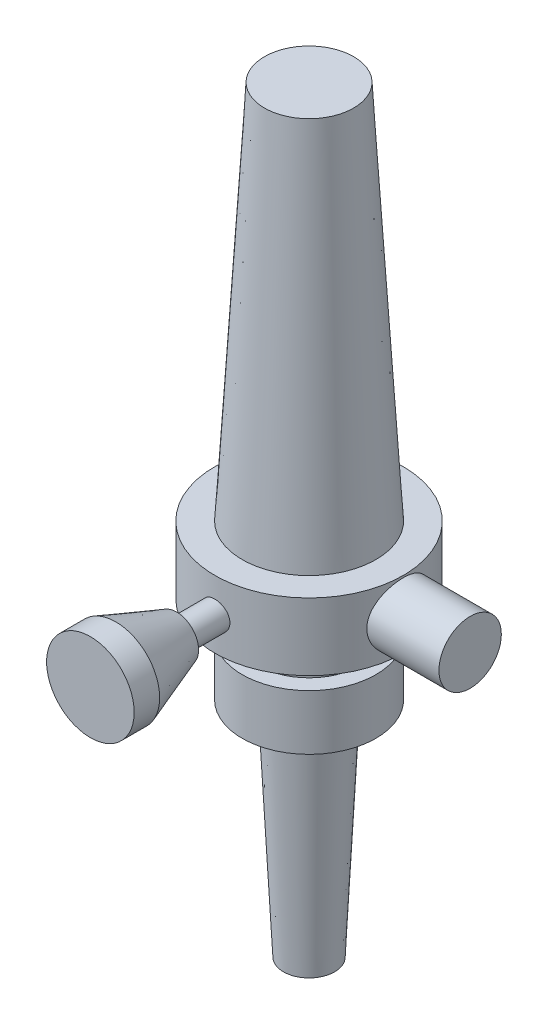
SolidWorks part; units mm, degrees
ref_plane "Спереди" through (0, 0, 0) normal (0, 0, 1) x (1, 0, 0)
ref_plane "Сверху" through (0, 0, 0) normal (0, 1, 0) x (1, 0, 0)
ref_plane "Справа" through (0, 0, 0) normal (1, 0, 0) x (0, 0, -1)
sketch "Эскиз1" plane through (0, 0, 0) normal (0, 0, 1) x (1, 0, 0)
  line L0 (0, 0) -> (0, 170) construction
  line L1 (0, 0) -> (5.7402, 0)
  line L2 (5.7402, 0) -> (8.1571, 50)
  line L3 (8.1571, 50) -> (15, 50)
  line L4 (15, 50) -> (15, 62.3867)
  line L5 (15, 62.3867) -> (11.4804, 62.3867)
  line L6 (11.4804, 62.3867) -> (11.4804, 69.6375)
  line L7 (11.4804, 69.6375) -> (21.148, 69.6375)
  line L8 (21.148, 69.6375) -> (21.148, 84.7432)
  line L9 (21.148, 84.7432) -> (15, 84.7432)
  line L10 (15, 84.7432) -> (10, 170)
  line L11 (10, 170) -> (0, 170)
  line L12 (0, 0) -> (0, 170)
  point P8 (15, 56.1934)
  point P15 (0, 0)
  point P16 (1.2048, 0)
  dimension "D1" = 170
  dimension "D2" = 50
  dimension "D3" = 15
  dimension "D4" = 10
  dimension "D5" = 15
revolve "Повернуть2" add sketch "Эскиз1" angle 360 about L0
ref_plane "Плоскость1" through (21.148, 0, 0) normal (1, 0, 0) x (0, 0, -1)
sketch "Эскиз2" plane through (21.148, 0, 0) normal (1, 0, 0) x (0, 0, -1)
  line L0 (0, 0) -> (0, 84.7432) construction
  line L1 (21.148, 84.7432) -> (-21.148, 84.7432) construction
  circle A0 centre (0, 77.2982) radius 7
extrude "Бобышка-Вытянуть1" add sketch "Эскиз2" along normal blind 15 and the other way blind 5
sketch "Эскиз3" plane through (0, 0, 0) normal (1, 0, 0) x (0, 0, -1)
  line L0 (-70.0308, 77) -> (29.6956, 77) construction
  line L1 (-49.0692, 77) -> (-49.0692, 86.8262)
  line L2 (-49.0692, 86.8262) -> (-43.3524, 86.8262)
  line L3 (-43.3524, 86.8262) -> (-29.6956, 81.9131)
  line L4 (-29.6956, 81.9131) -> (-29.6956, 80.1566)
  line L5 (-29.6956, 80.1566) -> (-20.1676, 80.1566)
  line L6 (-20.1676, 80.1566) -> (-20.1676, 77)
  line L7 (-49.0692, 77) -> (-20.1676, 77)
revolve "Повернуть3" add sketch "Эскиз3" angle 360 about L0
